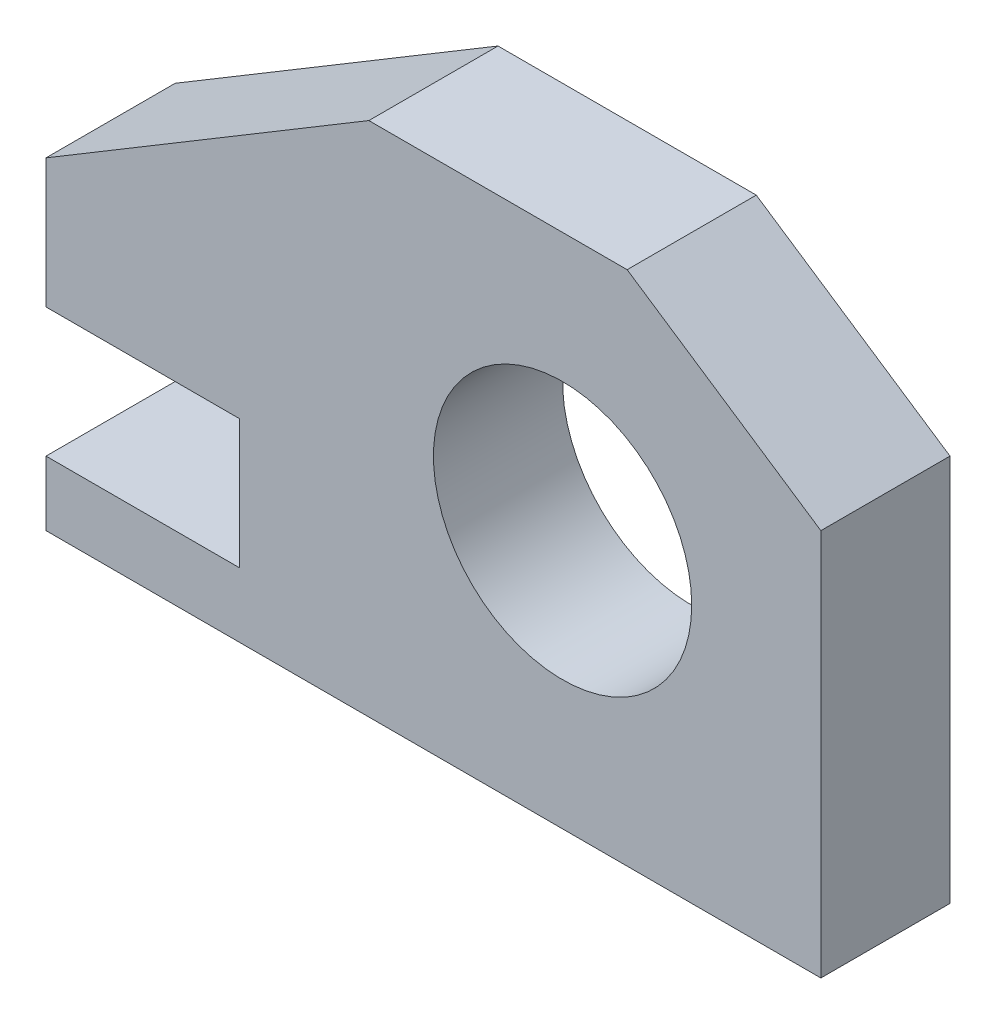
SolidWorks part; units mm, degrees
ref_plane "Front Plane" through (0, 0, 0) normal (0, 0, 1) x (1, 0, 0)
ref_plane "Top Plane" through (0, 0, 0) normal (0, 1, 0) x (1, 0, 0)
ref_plane "Right Plane" through (0, 0, 0) normal (1, 0, 0) x (0, 0, -1)
sketch "Sketch1" plane through (0, 0, 0) normal (0, 0, 1) x (1, 0, 0)
  line L0 (0, 0) -> (76.2, 0)
  line L1 (76.2, 0) -> (76.2, 38.1)
  line L2 (76.2, 38.1) -> (57.15, 50.8)
  line L3 (57.15, 50.8) -> (31.75, 50.8)
  line L4 (31.75, 50.8) -> (0, 31.75)
  line L5 (0, 31.75) -> (0, 19.05)
  line L6 (0, 19.05) -> (19.05, 19.05)
  line L7 (19.05, 19.05) -> (19.05, 6.35)
  line L8 (19.05, 6.35) -> (0, 6.35)
  line L9 (0, 6.35) -> (0, 0)
  point P2 (0, 0)
  dimension "D1" = 76.2
  dimension "D2" = 38.1
  dimension "D3" = 12.7
  dimension "D4" = 6.35
  dimension "D5" = 25.4
  dimension "D6" = 50.8
  dimension "D7" = 31.75
  dimension "D8" = 19.05
  dimension "D9" = 19.05
  dimension "D10" = 19.05
extrude "Boss-Extrude1" add sketch "Sketch1" along normal blind 12.7 contours L4 L5 L6 L7 L8 L9 L0 L1 L2 L3
sketch "Sketch2" plane through (0, 0, 12.7) normal (0, 0, 1) x (1, 0, 0)
  line L0 (76.2, 0) -> (76.2, 38.1) construction
  line L1 (0, 0) -> (76.2, 0) construction
  circle A0 centre (50.8, 25.4) radius 12.7
  dimension "D1" = 25.4
  dimension "D2" = 25.4
  dimension "D3" = 25.4
extrude "Cut-Extrude1" cut sketch "Sketch2" against normal through all
